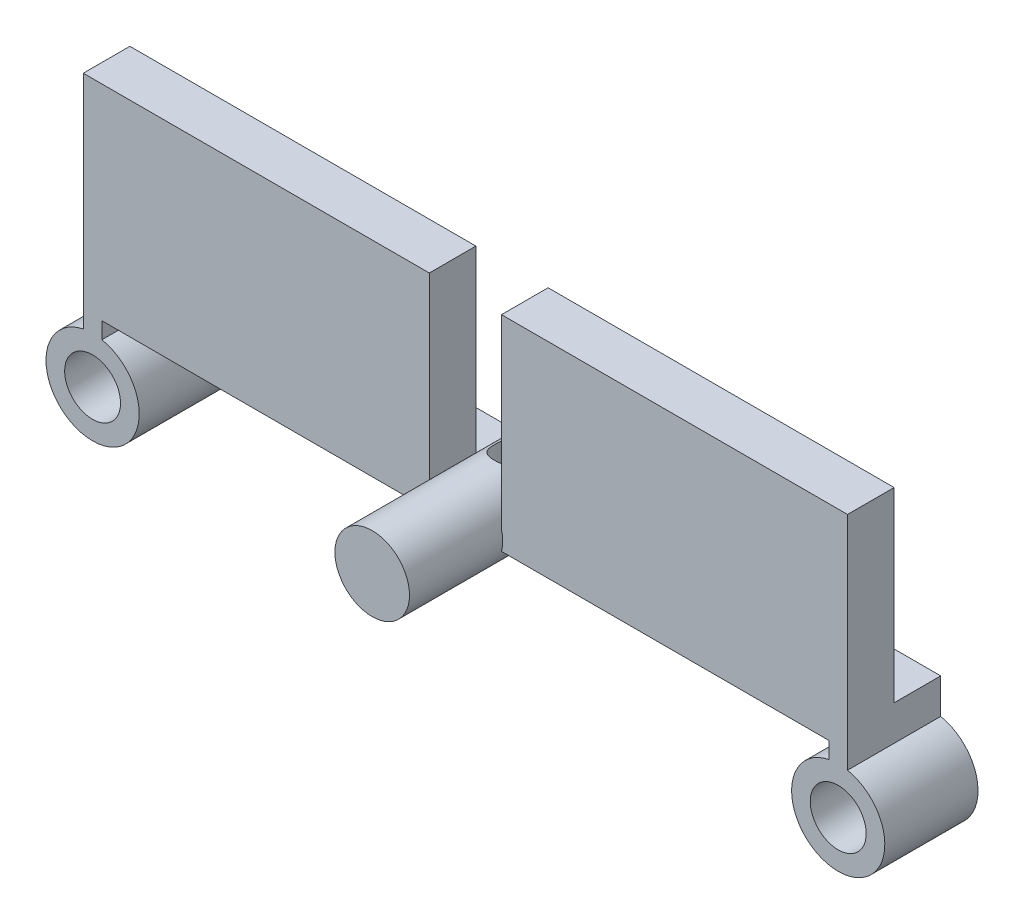
SolidWorks part; units mm, degrees
ref_plane "Front Plane" through (0, 0, 0) normal (0, 0, 1) x (1, 0, 0)
ref_plane "Top Plane" through (0, 0, 0) normal (0, 1, 0) x (1, 0, 0)
ref_plane "Right Plane" through (0, 0, 0) normal (1, 0, 0) x (0, 0, -1)
sketch "Sketch1" plane through (0, 0, 0) normal (0, 0, 1) x (1, 0, 0)
  circle A0 centre (0, 0) radius 6
  dimension "D1" = 12
extrude "Boss-Extrude1" add sketch "Sketch1" along normal blind 30
sketch "Sketch2" plane through (0, 0, 0) normal (0, 0, 1) x (1, 0, 0)
  line L0 (6, 0) -> (60, 0) construction
  line L1 (6.6, 0) -> (-6.6, 0) construction
  line L2 (60, 0) -> (60, -11.5) construction
  line L3 (6, -1.5) -> (58.5, -1.5)
  line L4 (58.5, -1.5) -> (58.5, -4.1515)
  line L5 (6, 1.5) -> (61.5, 1.5)
  line L6 (61.5, 1.5) -> (61.5, -4.1515)
  line L7 (6, 1.5) -> (5.8095, 1.5)
  line L8 (6, -1.5) -> (5.8095, -1.5)
  line L9 (0, -48.5414) -> (0, 48.5414) construction
  line L10 (61.5, 1.5) -> (61.5, -11.5) construction
  line L11 (58.5, -1.5) -> (58.5, -11.5) construction
  line L12 (-58.5, -1.5) -> (-58.5, -4.1515)
  line L13 (-61.5, 1.5) -> (-61.5, -4.1515)
  line L14 (-6, -1.5) -> (-58.5, -1.5)
  line L15 (-6, -1.5) -> (-5.8095, -1.5)
  line L16 (-6, 1.5) -> (-5.8095, 1.5)
  line L17 (-6, 1.5) -> (-61.5, 1.5)
  circle A0 centre (0, 0) radius 6 construction
  arc A1 (5.8095, -1.5) -> (5.8095, 1.5) centre (0, 0) ccw
  circle A2 centre (60, -11.5) radius 4.5
  arc A3 (58.5, -4.1515) -> (61.5, -4.1515) centre (60, -11.5) ccw
  circle A4 centre (-60, -11.5) radius 4.5
  arc A5 (-58.5, -4.1515) -> (-61.5, -4.1515) centre (-60, -11.5) cw
  arc A6 (-5.8095, -1.5) -> (-5.8095, 1.5) centre (0, 0) cw
  dimension "D5" = 9
  dimension "D6" = 15
  dimension "D1" = 54
  dimension "D2" = 11.5
  dimension "D3" = 1.5
  dimension "D4" = 1.5
extrude "Boss-Extrude2" add sketch "Sketch2" along normal blind 15
sketch "Sketch3" plane through (0, 0, 0) normal (0, 1, 0) x (1, 0, 0)
  line L0 (0, -48.5414) -> (0, 48.5414) construction
  line L1 (-13.75, 0) -> (13.75, 0) construction
  circle A0 centre (0, -7.5) radius 2.8686
  dimension "D1" = 7.5
extrude "Cut-Extrude1" cut sketch "Sketch3" against normal up to next and the other way up to next
sketch "Sketch4" plane through (0, 1.5, 0) normal (0, 1, 0) x (1, 0, 0)
  line L0 (-5.8095, -15) -> (-5.8095, 0) construction
  line L1 (-61.5, -15) -> (-5.8095, -15)
  line L2 (-61.5, -15) -> (-61.5, -7.5)
  line L3 (-61.5, -7.5) -> (-5.8095, -7.5)
  line L4 (-5.8095, -15) -> (-5.8095, -7.5)
  line L5 (0, -48.5414) -> (0, 48.5414) construction
  line L6 (5.8095, -15) -> (5.8095, -7.5)
  line L7 (61.5, -7.5) -> (5.8095, -7.5)
  line L8 (61.5, -15) -> (61.5, -7.5)
  line L9 (61.5, -15) -> (5.8095, -15)
extrude "Boss-Extrude3" add sketch "Sketch4" along normal blind 30
